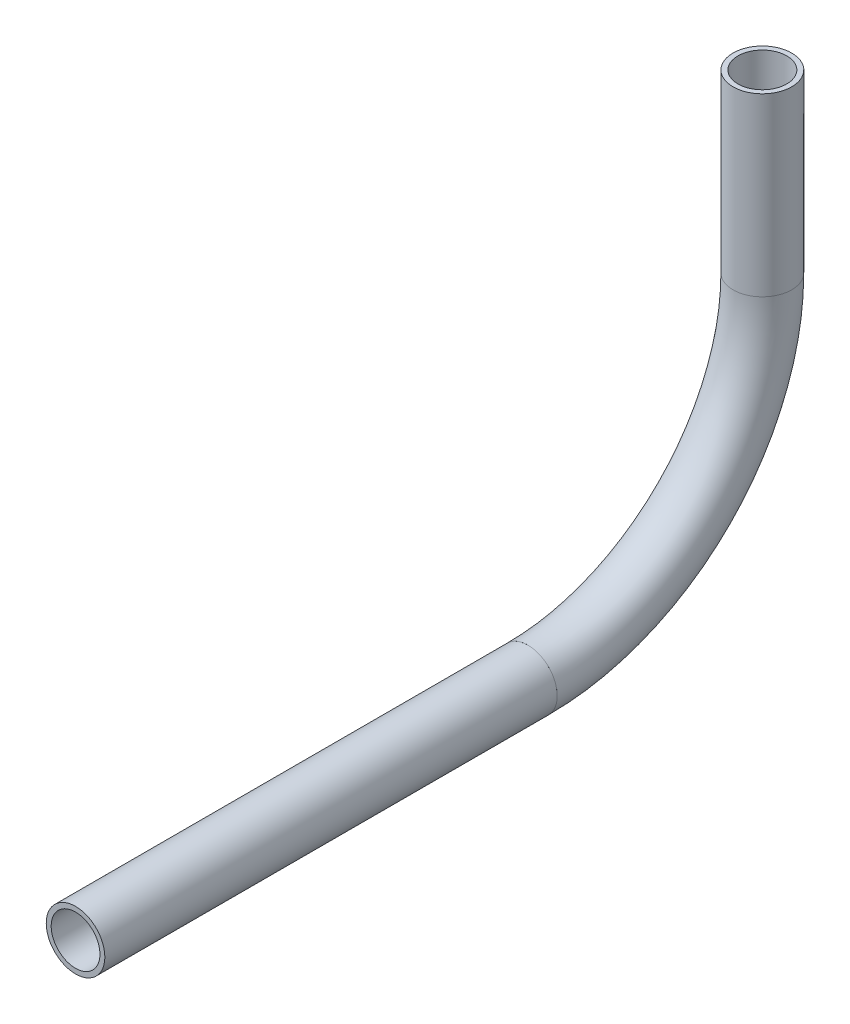
SolidWorks part; units mm, degrees
ref_plane "Front Plane" through (0, 0, 0) normal (0, 0, 1) x (1, 0, 0)
ref_plane "Top Plane" through (0, 0, 0) normal (0, 1, 0) x (1, 0, 0)
ref_plane "Right Plane" through (0, 0, 0) normal (1, 0, 0) x (0, 0, -1)
sketch "Sketch3" plane through (0, 0, 0) normal (1, 0, 0) x (0, 0, -1)
  line L0 (-278.7482, -242.6492) -> (-278.7482, -280.7492)
  line L1 (-329.5482, -331.5492) -> (-427.5775, -331.5492)
  arc A0 (-278.7482, -280.7492) -> (-329.5482, -331.5492) centre (-329.5482, -280.7492) cw
  point P2 (-419.4454, -345.2194)
  point P6 (-421.3028, -342.8581)
  point P7 (-422.3146, -343.2731)
  point P8 (0, 0)
  point P11 (0, 0)
  point P12 (-427.5775, -331.5492)
  point P14 (-421.7988, -352.5667)
  dimension "D1" = 50.8
  dimension "D2" = 38.1
other "Pipe 0.5 SCH 40(1)"
ref_plane "Plane1" through (0, -242.6492, 278.7482) normal (0, -1, 0) x (0, 0, -1)
sketch "Sketch1" plane through (0, -242.6492, 278.7482) normal (0, -1, 0) x (0, 0, -1)
  circle A0 centre (0, 0) radius 6.35
  circle A1 centre (0, 0) radius 5.2832
  point P5 (0, 0)
  dimension "In_dia" = 12.7
  dimension "Out_dia" = 10.5664
